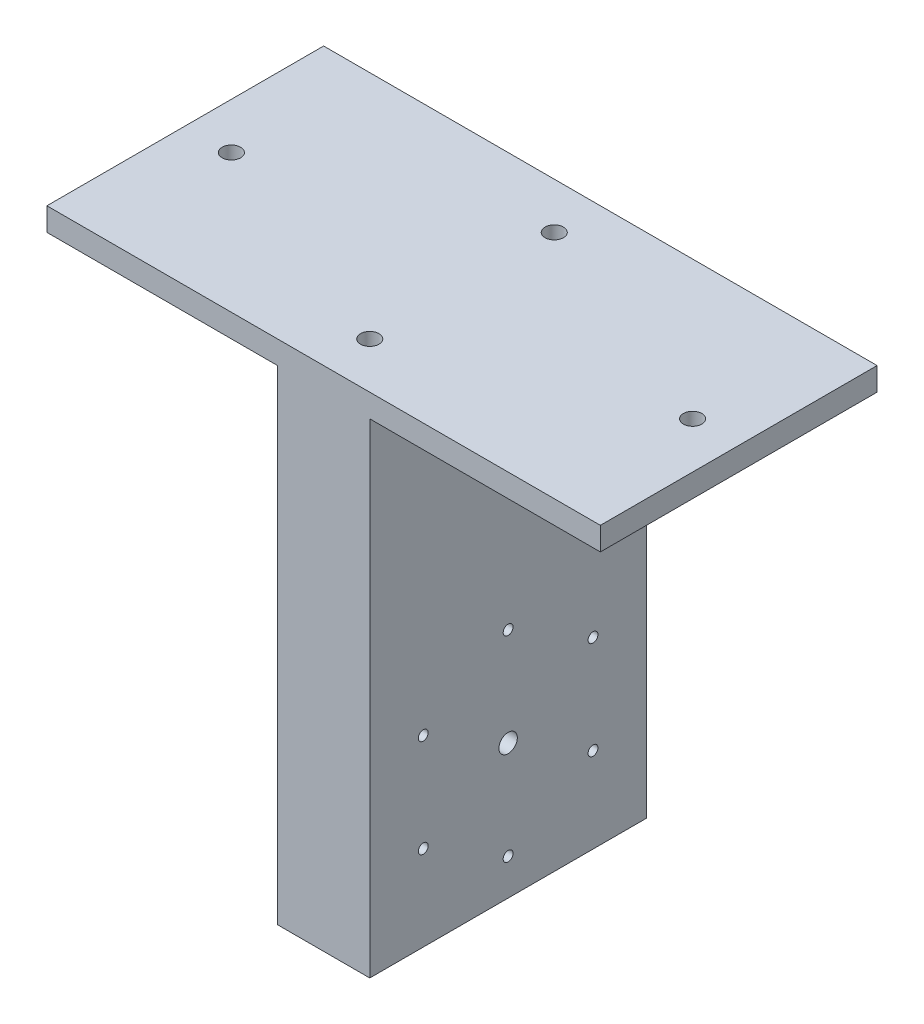
SolidWorks part; units mm, degrees
ref_plane "前视基准面" through (0, 0, 0) normal (0, 0, 1) x (1, 0, 0)
ref_plane "上视基准面" through (0, 0, 0) normal (0, 1, 0) x (1, 0, 0)
ref_plane "右视基准面" through (0, 0, 0) normal (1, 0, 0) x (0, 0, -1)
other "Configuration Table"
sketch "草图1" plane through (0, 0, 0) normal (0, 0, 1) x (1, 0, 0)
  line L0 (0, 0) -> (40, 0)
  line L1 (40, 0) -> (40, 210)
  line L2 (40, 210) -> (140, 210)
  line L3 (140, 210) -> (140, 220)
  line L4 (140, 220) -> (-100, 220)
  line L5 (-100, 220) -> (-100, 210)
  line L6 (-100, 210) -> (0, 210)
  line L7 (0, 210) -> (0, 0)
  dimension "D1" = 40
  dimension "D2" = 210
  dimension "D3" = 100
  dimension "D4" = 100
  dimension "D5" = 10
extrude "凸台-拉伸1" add sketch "草图1" along normal blind 120 contours L7 L0 L1 L2 L3 L4 L5 L6
sketch "草图2" plane through (40, 0, 0) normal (1, 0, 0) x (0, 0, -1)
  line L1 (-60, 0) -> (-60, 59.6415) construction
  line L2 (-120, 0) -> (0, 0) construction
  line L3 (-108.25, 10) -> (-11.75, 10)
  line L4 (-108.25, 10) -> (-108.25, 106.5)
  line L5 (-108.25, 106.5) -> (-11.75, 106.5)
  line L6 (-11.75, 10) -> (-11.75, 106.5)
  line L7 (-108.25, 10) -> (-11.75, 106.5) construction
  line L8 (-108.25, 106.5) -> (-11.75, 10) construction
  circle A0 centre (-60, 58.25) radius 4
  circle A1 centre (-60, 100.75) radius 2.139
  circle A2 centre (-23.1939, 79.5) radius 2.139
  circle A3 centre (-23.1939, 37) radius 2.139
  circle A4 centre (-60, 15.75) radius 2.139
  circle A5 centre (-96.8061, 37) radius 2.139
  circle A6 centre (-96.8061, 79.5) radius 2.139
  point P0 (-60, 58.25)
  point P26 (-60, 58.25)
  dimension "D1" = 96.5
  dimension "D2" = 96.5
  dimension "D3" = 10
  dimension "D4" = 42.5
  dimension "D5" = 6
extrude "切除-拉伸1" cut sketch "草图2" against normal blind 100 contours A2 | A1 | A3 | A4 | A5 | A6 | A0
sketch "草图3" plane through (0, 220, 0) normal (0, 1, 0) x (1, 0, 0)
  line L0 (-100, -60) -> (140, -60) construction
  line L3 (20, 0) -> (20, -120) construction
  circle A0 centre (-80, -60) radius 4
  circle A1 centre (20, -20) radius 4
  circle A2 centre (120, -60) radius 4
  circle A3 centre (20, -100) radius 4
  dimension "D1" = 40
  dimension "D2" = 40
  dimension "D3" = 100
  dimension "D4" = 100
extrude "切除-拉伸2" cut sketch "草图3" against normal blind 10 and the other way through all
